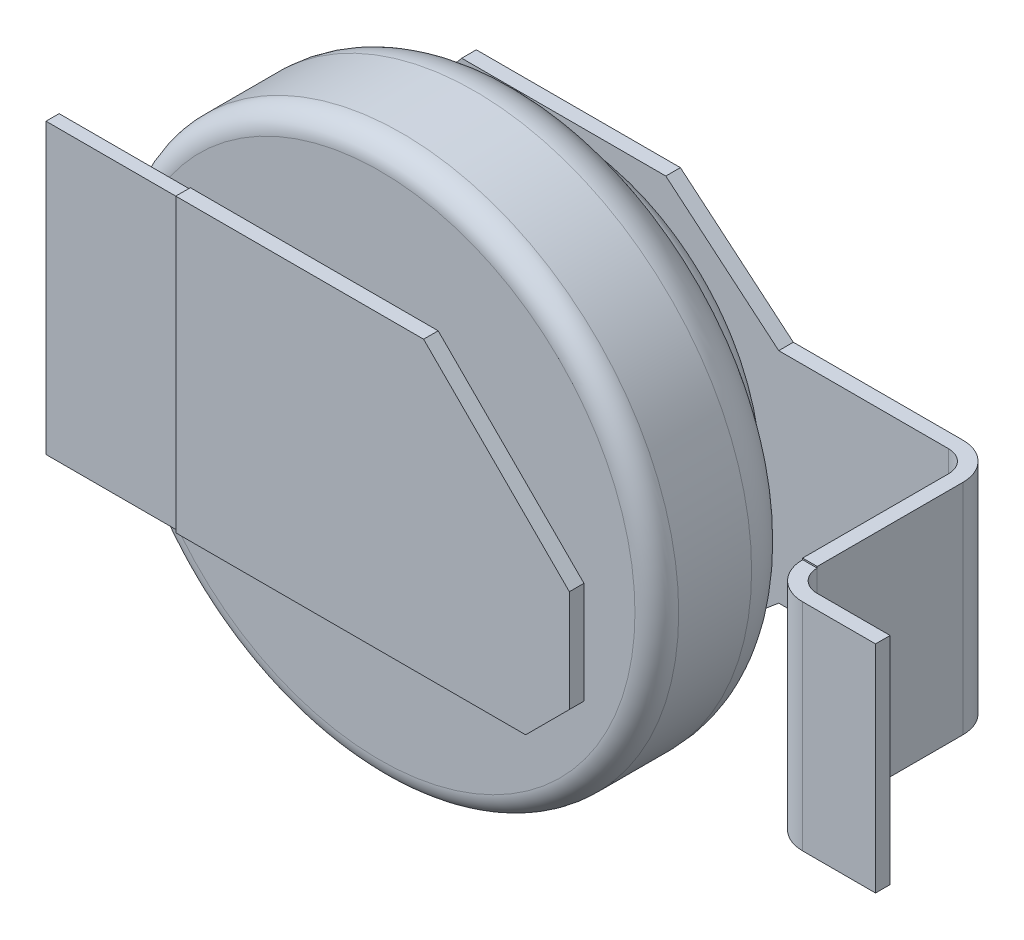
SolidWorks part; units mm, degrees
ref_plane "Front Plane" through (0, 0, 0) normal (0, 0, 1) x (1, 0, 0)
ref_plane "Top Plane" through (0, 0, 0) normal (0, 1, 0) x (1, 0, 0)
ref_plane "Right Plane" through (0, 0, 0) normal (1, 0, 0) x (0, 0, -1)
sketch "Sketch1" plane through (0, 0, 0) normal (0, 1, 0) x (1, 0, 0)
  line L0 (0, 0) -> (0, 1.3)
  line L1 (0, 0) -> (-1.75, 0)
  line L2 (-1.9, 0.15) -> (-1.9, 0.65)
  line L3 (-1.55, 1) -> (-1.5, 1)
  line L4 (-1.5, 1) -> (-1.5, 1.02)
  line L5 (-1.42, 1.1) -> (-1.4, 1.1)
  line L6 (-1.4, 1.1) -> (-1.4, 1.15)
  line L7 (-1.25, 1.3) -> (0, 1.3)
  arc A0 (-1.75, 0) -> (-1.9, 0.15) centre (-1.75, 0.15) cw
  arc A1 (-1.9, 0.65) -> (-1.55, 1) centre (-1.55, 0.65) cw
  arc A2 (-1.5, 1.02) -> (-1.42, 1.1) centre (-1.42, 1.02) cw
  arc A3 (-1.4, 1.15) -> (-1.25, 1.3) centre (-1.25, 1.15) cw
  dimension "D6" = 1.9
  dimension "D3" = 0.08
  dimension "D5" = 0.35
  dimension "D7" = 0.15
  dimension "D10" = 0.15
  dimension "D1" = 1.3
  dimension "D2" = 1
  dimension "D4" = 0.2
  dimension "D8" = 0.1
  dimension "D9" = 1.4
revolve "Revolve1" add sketch "Sketch1" angle 360 about L0
sketch "Sketch2" plane through (0, 0, 0) normal (0, 0, 1) x (1, 0, 0)
  line L0 (-2.2, 1) -> (-2.2, -1)
  line L1 (-2.2, -1) -> (1.1, -1)
  line L2 (1.1, -1) -> (1.4, -0.7)
  line L3 (1.4, -0.7) -> (1.4, 0)
  line L4 (1.4, 0) -> (0.4, 1)
  line L5 (0.4, 1) -> (-2.2, 1)
  line L6 (0, 0) -> (1.4, 0) construction
  line L7 (0, 0) -> (-2.2, 0) construction
  circle A0 centre (0, 0) radius 1.9 construction
  point P2 (-1.9, 0)
  dimension "D1" = 0.3
  dimension "D2" = 2
  dimension "D3" = 45
  dimension "D4" = 1.4
  dimension "D5" = 0.7
extrude "Boss-Extrude1" add sketch "Sketch2" along normal blind 0.1
sketch "Sketch4" plane through (0, 0, 0.1) normal (0, 0, 1) x (1, 0, 0)
  line L0 (-2.2, -1) -> (1.1, -1) construction
  line L1 (-2.2, 1) -> (-1.3, 1)
  line L2 (-2.2, 1) -> (-2.2, -1)
  line L3 (-2.2, -1) -> (-1.3, -1)
  line L4 (-1.3, 1) -> (-1.3, -1)
  dimension "D1" = 0.9
extrude "Cut-Extrude1" cut sketch "Sketch4" against normal blind 0.01
sketch "Sketch5" plane through (0, 1, 0) normal (0, 1, 0) x (1, 0, 0)
  line L1 (-2.2, 0) -> (-1.3, 0)
  line L2 (-2.2, 0) -> (-2.2, -0.09)
  line L3 (-2.2, -0.09) -> (-1.3, -0.09)
  line L4 (-1.3, 0) -> (-1.3, -0.09)
extrude "Cut-Extrude2" cut sketch "Sketch5" against normal blind 0.01
sketch "Sketch6" plane through (0, -1, 0) normal (0, -1, 0) x (1, 0, 0)
  line L1 (-2.2, 0) -> (-1.3, 0)
  line L2 (-2.2, 0) -> (-2.2, 0.09)
  line L3 (-2.2, 0.09) -> (-1.3, 0.09)
  line L4 (-1.3, 0) -> (-1.3, 0.09)
extrude "Cut-Extrude3" cut sketch "Sketch6" against normal blind 0.01
sketch "Sketch7" plane through (0, 0, -1.3) normal (0, 0, -1) x (-1, 0, 0)
  line L0 (1.2, 0.85) -> (1.2, -0.85)
  line L1 (1.2, -0.85) -> (0.7385, -1.4)
  line L2 (0.7385, -1.4) -> (-0.6615, -1.4)
  line L3 (-0.6615, -1.4) -> (-1.4361, -0.75)
  line L4 (-1.4361, -0.75) -> (-2.5, -0.75)
  line L5 (-2.5, -0.75) -> (-2.5, 0.75)
  line L6 (-2.5, 0.75) -> (-1.4361, 0.75)
  line L7 (-1.4361, 0.75) -> (-0.6615, 1.4)
  line L8 (-0.6615, 1.4) -> (0.7385, 1.4)
  line L9 (0.7385, 1.4) -> (1.2, 0.85)
  line L10 (1.2, 0) -> (0, 0) construction
  line L11 (0, 0) -> (-2.5, 0) construction
  line L12 (0.7385, 1.4) -> (0.7385, -1.4) construction
  dimension "D1" = 40
  dimension "D2" = 2.8
  dimension "D3" = 1.7
  dimension "D4" = 1.5
  dimension "D5" = 2.5
  dimension "D6" = 1.4
  dimension "D7" = 40
  dimension "D8" = 1.2
extrude "Boss-Extrude2" add sketch "Sketch7" along normal blind 0.1
sketch "Sketch8" plane through (0, 0, 0) normal (0, 1, 0) x (1, 0, 0)
  line L0 (2.5, 1.35) -> (2.6, 1.35)
  line L1 (2.5, 1.4) -> (2.5, 1.3) construction
  line L2 (2.8, 1.15) -> (2.8, 0.15)
  line L3 (3, -0.05) -> (3.5, -0.05)
  line L4 (-2.2, 0) -> (-2.2, -0.09) construction
  line L5 (1.4, -0.1) -> (0.4, -0.1) construction
  arc A0 (3, -0.05) -> (2.8, 0.15) centre (3, 0.15) cw
  arc A1 (2.8, 1.15) -> (2.6, 1.35) centre (2.6, 1.15) ccw
  point P4 (-2.2, -0.045)
  point P11 (2.8, -0.05)
  dimension "D3" = 0.2
  dimension "D1" = 5.7
  dimension "D2" = 0.7
  dimension "D4" = 0.05
sketch "Sketch9" plane through (2.5, 0, 0) normal (1, 0, 0) x (0, 0, -1)
  line L1 (1.3, 0.75) -> (1.4, 0.75)
  line L2 (1.3, 0.75) -> (1.3, -0.75)
  line L3 (1.3, -0.75) -> (1.4, -0.75)
  line L4 (1.4, 0.75) -> (1.4, -0.75)
sweep "Sweep1" add profiles "Sketch9" path "Sketch8"
sketch "Sketch10" plane through (0, 0.75, 0) normal (0, 1, 0) x (1, 0, 0)
  line L1 (3.5, -0.1) -> (2.7, -0.1)
  line L2 (3.5, -0.1) -> (3.5, 0.15)
  line L3 (3.5, 0.15) -> (2.7, 0.15)
  line L4 (2.7, -0.1) -> (2.7, 0.15)
  dimension "D1" = 0.25
  dimension "D2" = 0.8
extrude "Cut-Extrude4" cut sketch "Sketch10" against normal blind 0.01
sketch "Sketch11" plane through (0, -0.75, 0) normal (0, -1, 0) x (1, 0, 0)
  line L1 (3.5, 0.1) -> (2.7, 0.1)
  line L2 (3.5, 0.1) -> (3.5, -0.15)
  line L3 (3.5, -0.15) -> (2.7, -0.15)
  line L4 (2.7, 0.1) -> (2.7, -0.15)
  dimension "D1" = 0.25
  dimension "D2" = 0.8
extrude "Cut-Extrude5" cut sketch "Sketch11" against normal blind 0.01
